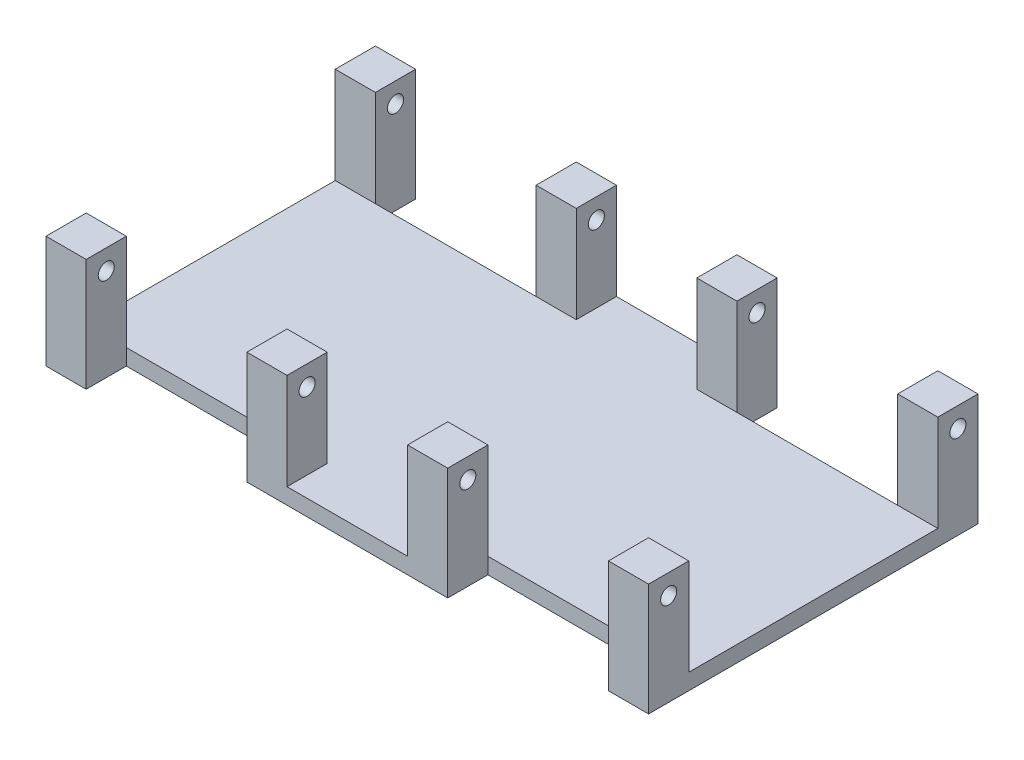
SolidWorks part; units mm, degrees
ref_plane "Front Plane" through (0, 0, 0) normal (0, 0, 1) x (1, 0, 0)
ref_plane "Top Plane" through (0, 0, 0) normal (0, 1, 0) x (1, 0, 0)
ref_plane "Right Plane" through (0, 0, 0) normal (1, 0, 0) x (0, 0, -1)
sketch "Sketch1" plane through (0, 0, 0) normal (0, 1, 0) x (1, 0, 0)
  line L1 (-65, -41) -> (65, -41)
  line L2 (-65, -41) -> (-65, 41)
  line L3 (-65, 41) -> (65, 41)
  line L4 (65, -41) -> (65, 41)
  line L5 (-65, -41) -> (65, 41) construction
  line L6 (-65, 41) -> (65, -41) construction
  point P0 (0, 0)
  dimension "D1" = 130
  dimension "D2" = 82
extrude "Boss-Extrude1" add sketch "Sketch1" along normal blind 4
sketch "Sketch2" plane through (0, 4, 0) normal (0, 1, 0) x (1, 0, 0)
  line L0 (-15.4, 0) -> (15.4, 0) construction
  line L1 (-65, 41) -> (-25, 41)
  line L2 (-65, 41) -> (-65, 31)
  line L3 (-65, 31) -> (-25, 31)
  line L4 (-25, 41) -> (-25, 31)
  line L5 (65, 41) -> (25, 41)
  line L6 (65, 41) -> (65, 31)
  line L7 (65, 31) -> (25, 31)
  line L8 (25, 41) -> (25, 31)
  line L9 (25, -41) -> (25, -31)
  line L10 (65, -31) -> (25, -31)
  line L11 (65, -41) -> (65, -31)
  line L12 (65, -41) -> (25, -41)
  line L13 (-25, -41) -> (-25, -31)
  line L14 (-65, -31) -> (-25, -31)
  line L15 (-65, -41) -> (-65, -31)
  line L16 (-65, -41) -> (-25, -41)
  dimension "D1" = 10
  dimension "D2" = 40
extrude "Cut-Extrude1" cut sketch "Sketch2" against normal blind 24
sketch "Sketch3" plane through (0, 4, 0) normal (0, 1, 0) x (1, 0, 0)
  line L0 (-65, 31) -> (-65, 41)
  line L1 (75, -41) -> (-75, -41)
  line L2 (75, -41) -> (75, 41)
  line L3 (75, 41) -> (-75, 41)
  line L4 (-75, -41) -> (-75, 41)
  line L5 (75, -41) -> (-75, 41) construction
  line L6 (75, 41) -> (-75, -41) construction
  line L7 (-65, -31) -> (-65, -41)
  line L8 (65, 41) -> (65, 31)
  line L9 (65, -41) -> (65, -31)
  line L12 (-65, 31) -> (-65, -31)
  line L13 (-65, -31) -> (-25, -31)
  line L14 (-25, -31) -> (-25, -41)
  line L15 (-25, -41) -> (25, -41)
  line L16 (25, -41) -> (25, -31)
  line L17 (25, -31) -> (65, -31)
  line L18 (65, -31) -> (65, 31)
  line L19 (65, 31) -> (25, 31)
  line L20 (25, 31) -> (25, 41)
  line L21 (25, 41) -> (-25, 41)
  line L22 (-25, 41) -> (-25, 31)
  line L23 (-25, 31) -> (-65, 31)
  line L24 (-65, 31) -> (-65, -31)
  line L25 (-65, -31) -> (-25, -31)
  line L26 (-25, -31) -> (-25, -41)
  line L27 (-25, -41) -> (25, -41)
  line L28 (25, -41) -> (25, -31)
  line L29 (25, -31) -> (65, -31)
  line L30 (65, -31) -> (65, 31)
  line L31 (65, 31) -> (25, 31)
  line L32 (25, 31) -> (25, 41)
  line L33 (25, 41) -> (-25, 41)
  line L34 (-25, 41) -> (-25, 31)
  line L35 (-25, 31) -> (-65, 31)
  point P2 (0, 0)
  line M17 (-65, 31) -> (-65, -31)
  line M23 (65, -31) -> (65, 31)
  dimension "D2" = 10
  dimension "D3" = 82
  dimension "D1" = 0
extrude "Boss-Extrude2" add sketch "Sketch3" against normal blind 4 contours L7 L0 L3 L4 L1 M17 | L9 L1 L2 L3 L8 M23
sketch "Sketch4" plane through (0, 4, 0) normal (0, 1, 0) x (1, 0, 0)
  line L0 (-65, 31) -> (-25, 31) construction
  line L1 (-75, 41) -> (-65, 41)
  line L2 (-75, 41) -> (-75, 31)
  line L3 (-75, 31) -> (-65, 31)
  line L4 (-65, 41) -> (-65, 31)
  line L5 (-25, 41) -> (-15, 41)
  line L6 (-25, 41) -> (-25, 31)
  line L7 (-25, 31) -> (-15, 31)
  line L8 (-15, 41) -> (-15, 31)
  line L9 (0, -2.2) -> (0, 2.2) construction
  line L10 (15, 41) -> (15, 31)
  line L11 (25, 31) -> (15, 31)
  line L12 (25, 41) -> (25, 31)
  line L13 (25, 41) -> (15, 41)
  line L14 (65, 41) -> (65, 31)
  line L15 (75, 31) -> (65, 31)
  line L16 (75, 41) -> (75, 31)
  line L17 (75, 41) -> (65, 41)
  line L18 (-2.2, 0) -> (2.2, 0) construction
  line L19 (75, -41) -> (65, -41)
  line L20 (75, -41) -> (75, -31)
  line L21 (75, -31) -> (65, -31)
  line L22 (65, -41) -> (65, -31)
  line L23 (25, -41) -> (15, -41)
  line L24 (25, -41) -> (25, -31)
  line L25 (25, -31) -> (15, -31)
  line L26 (15, -41) -> (15, -31)
  line L27 (-15, -41) -> (-15, -31)
  line L28 (-25, -31) -> (-15, -31)
  line L29 (-25, -41) -> (-25, -31)
  line L30 (-25, -41) -> (-15, -41)
  line L31 (-65, -41) -> (-65, -31)
  line L32 (-75, -31) -> (-65, -31)
  line L33 (-75, -41) -> (-75, -31)
  line L34 (-75, -41) -> (-65, -41)
extrude "Boss-Extrude3" add sketch "Sketch4" along normal blind 24
sketch "Sketch5" plane through (-75, 0, 0) normal (-1, 0, 0) x (0, 0, 1)
  line L0 (-31, 28) -> (-31, 4) construction
  line L1 (41, 0) -> (-41, 0) construction
  line L2 (0, -2.2) -> (0, 2.2) construction
  circle A0 centre (-36, 23) radius 2
  circle A1 centre (36, 23) radius 2
  dimension "D1" = 4
  dimension "D2" = 5
  dimension "D3" = 23
extrude "Cut-Extrude2" cut sketch "Sketch5" against normal through all
